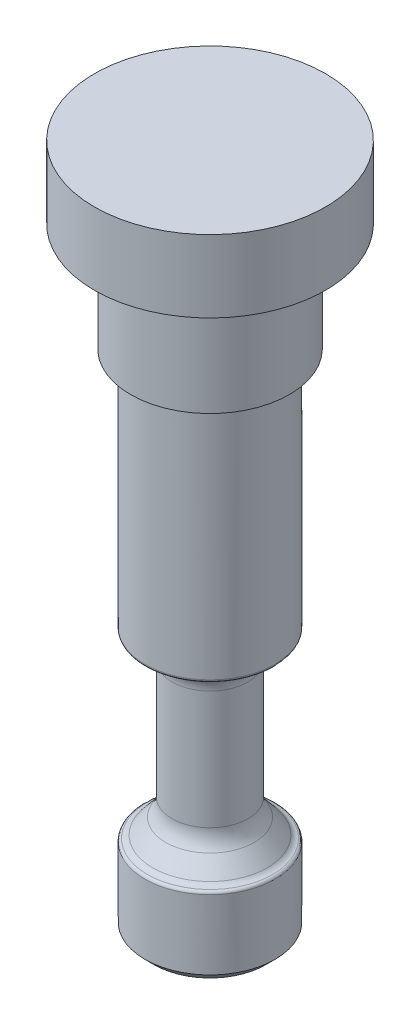
SolidWorks part; units mm, degrees
ref_plane "Front Plane" through (0, 0, 0) normal (0, 0, 1) x (1, 0, 0)
ref_plane "Top Plane" through (0, 0, 0) normal (0, 1, 0) x (1, 0, 0)
ref_plane "Right Plane" through (0, 0, 0) normal (1, 0, 0) x (0, 0, -1)
sketch "Sketch1" plane through (0, 0, 0) normal (0, 1, 0) x (1, 0, 0)
  circle A0 centre (0, 0) radius 5.715
  dimension "D1" = 11.43
extrude "main" add sketch "Sketch1" along normal blind 44.45
chamfer "Chamfer1" distance 0.7937 1 edges at (0, 0, 5.715)
sketch "Sketch2" plane through (0, 0, 0) normal (1, 0, 0) x (0, 0, -1)
  line L0 (5.715, 0.7938) -> (5.715, 44.45) construction
  line L1 (-5.715, 44.45) -> (-5.715, 0.7938) construction
  line L2 (5.715, 44.45) -> (-5.715, 44.45) construction
  line L3 (5.715, 0.7938) -> (5.715, 44.45)
  line L4 (-5.715, 44.45) -> (-5.715, 0.7938)
  line L5 (5.715, 44.45) -> (-5.715, 44.45)
  line L6 (-3.8909, 8.7881) -> (-5.0327, 7.4273)
  line L7 (-5.715, 7.1438) -> (-5.6408, 7.1438)
  line L8 (-5.715, 7.1438) -> (-5.715, 23.0188)
  line L9 (-5.715, 23.0188) -> (-5.6197, 23.0188)
  line L10 (-3.3337, 10.3188) -> (-3.3337, 20.7328)
  arc A0 (-5.6197, 23.0188) -> (-3.3337, 20.7328) centre (-5.6197, 20.7328) cw
  arc A2 (-3.3337, 10.3188) -> (-3.8909, 8.7881) centre (-5.715, 10.3188) cw
  arc A4 (-5.6408, 7.1438) -> (-5.0327, 7.4273) centre (-5.6408, 7.9375) ccw
  point P12 (-3.3337, 7.1438)
  dimension "D4" = 2.286
  dimension "D5" = 2.3812
  dimension "D6" = 0.7937
  dimension "D1" = 15.875
  dimension "D2" = 2.3812
  dimension "D3" = 6.35
  dimension "D7" = 3.175
  dimension "D8" = 40
ref_axis "Axis1" through (0, 44.45, 0) along (0, -1, 0)
revolve "Cut-Revolve1" cut sketch "Sketch2" angle 360 about axis through (0, 44.45, 0) along (0, -1, 0)
fillet "Fillet1" radius 0.254 2 edges at (0, 7.1438, 5.715) (0, 23.0188, 5.715)
sketch "Sketch6" plane through (0, 44.45, 0) normal (0, 1, 0) x (1, 0, 0)
  circle A0 centre (0, 0) radius 6.985
  dimension "D1" = 13.97
extrude "spring_stabilizer" add sketch "Sketch6" along normal blind 9.525
sketch "Sketch3" plane through (0, 53.975, 0) normal (0, 1, 0) x (1, 0, 0)
  circle A0 centre (0, 0) radius 10.16
  circle A3 centre (0, 0) radius 6.985 construction
  circle A4 centre (0, 0) radius 6.985
  dimension "D1" = 3.175
extrude "top_cap" add sketch "Sketch3" along normal blind 6.35
fillet "Fillet2" radius 1.27 1 edges at (0, 53.975, 6.985)
sketch "Sketch4" [suppressed] plane through (0, 0, 0) normal (0, -1, 0) x (1, 0, 0)
  line L0 (-2.7079, 5.0327) -> (2.7079, 5.0327)
  line L1 (-2.7079, -5.0327) -> (2.7079, -5.0327)
  circle A0 centre (0, 0) radius 5.715 construction
  circle A1 centre (0, 0) radius 5.715
  circle A2 centre (0, 0) radius 5.0327 construction
  circle A3 centre (0, 0) radius 5.0327
  circle M3 centre (0, 0) radius 4.9213
  dimension "D1" = 5.4159
ref_point "Point1"
extrude "spring_atchmnt_flat" [suppressed] cut sketch "Sketch4" against normal up to vertex contours L0 M3 | L1 M3
sketch "Sketch5" [suppressed] plane through (0, 0, 5.0327) normal (0, 0, 1) x (1, 0, 0)
  line L1 (-2.7079, 6.9053) -> (-2.7079, 0.7937) construction
  circle A0 centre (0, 3.8495) radius 1.5875
  point P7 (-2.7079, 3.8495)
  dimension "D1" = 3.175
extrude "spring_atchmnt_hole" [suppressed] cut sketch "Sketch5" against normal through all
